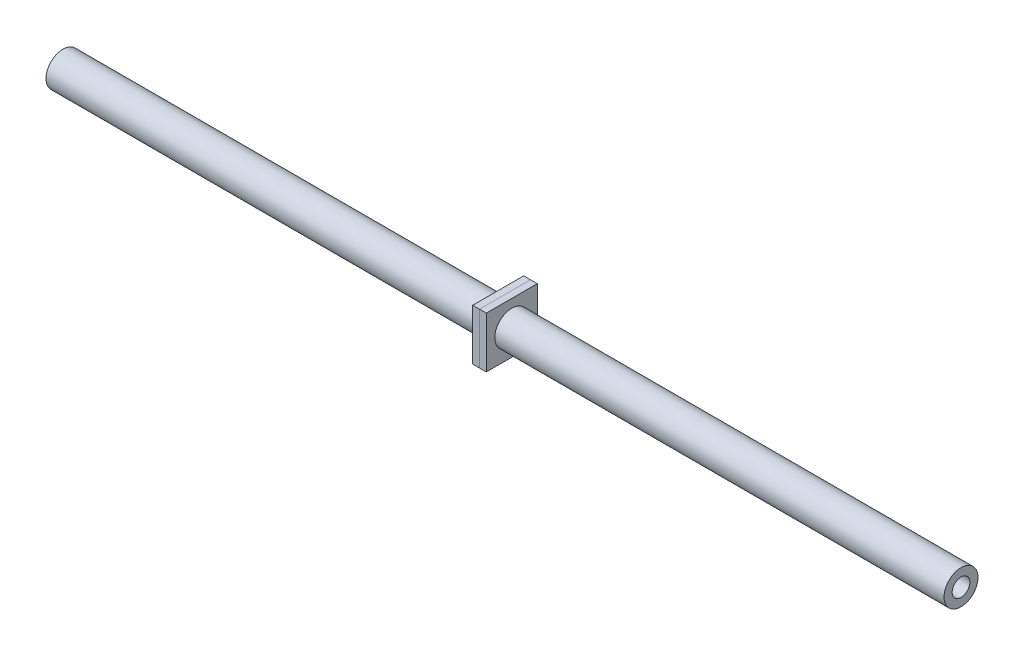
SolidWorks part; units mm, degrees
material "AISI 4130 Steel, normalized at 870C"
ref_plane "Front Plane" through (0, 0, 0) normal (0, 0, 1) x (1, 0, 0)
ref_plane "Top Plane" through (0, 0, 0) normal (0, 1, 0) x (1, 0, 0)
ref_plane "Right Plane" through (0, 0, 0) normal (1, 0, 0) x (0, 0, -1)
sketch "Pull Rod" plane through (0, 0, 0) normal (0, 0, 1) x (1, 0, 0)
  line L0 (0, 0) -> (335.4642, 0)
  line L1 (0, 0) -> (-27.8003, 0) construction
  line L2 (335.4642, 0) -> (363.2645, 0) construction
  dimension "D1" = 27.8003
  dimension "D2" = 391.0648
other "Pull Rod Member"
ref_plane "Plane1" through (0, 0, 0) normal (1, 0, 0) x (0, 1, 0)
sketch "Sketch11" plane through (0, 0, 0) normal (1, 0, 0) x (0, 1, 0)
  circle A0 centre (0, 0) radius 6.35
  circle A1 centre (0, 0) radius 3.302
  point P3 (0, 0)
  dimension "D1" = 12.7
  dimension "D2" = 3.048
sketch "Sketch12" plane through (0, 0, 0) normal (1, 0, 0) x (0, 0, -1)
  line L1 (9.525, 9.525) -> (-9.525, 9.525)
  line L2 (9.525, 9.525) -> (9.525, -9.525)
  line L3 (9.525, -9.525) -> (-9.525, -9.525)
  line L4 (-9.525, 9.525) -> (-9.525, -9.525)
  line L5 (9.525, 9.525) -> (-9.525, -9.525) construction
  line L6 (9.525, -9.525) -> (-9.525, 9.525) construction
  circle A0 centre (0, 0) radius 6.35 construction
  circle A1 centre (0, 0) radius 6.35
  dimension "D1" = 19.05
extrude "Pull Rod Nut 1" add sketch "Sketch12" along normal blind 2.54 from offset 165.1 separate body
sketch "Sketch14" plane through (0, 0, 0) normal (1, 0, 0) x (0, 0, -1)
  line L0 (9.525, 9.525) -> (-9.525, 9.525) construction
  line L1 (9.525, 9.525) -> (9.525, -9.525) construction
  line L2 (9.525, -9.525) -> (-9.525, -9.525) construction
  line L3 (-9.525, 9.525) -> (-9.525, -9.525) construction
  line L4 (9.525, 9.525) -> (-9.525, 9.525)
  line L5 (9.525, 9.525) -> (9.525, -9.525)
  line L6 (9.525, -9.525) -> (-9.525, -9.525)
  line L7 (-9.525, 9.525) -> (-9.525, -9.525)
  circle A0 centre (0, 0) radius 6.35 construction
  circle A1 centre (0, 0) radius 6.35
extrude "Pull Rod Nut 2" add sketch "Sketch14" against normal blind 2.54 from surface at 165.1 separate body starting at face at (165.1, 0, 0)
